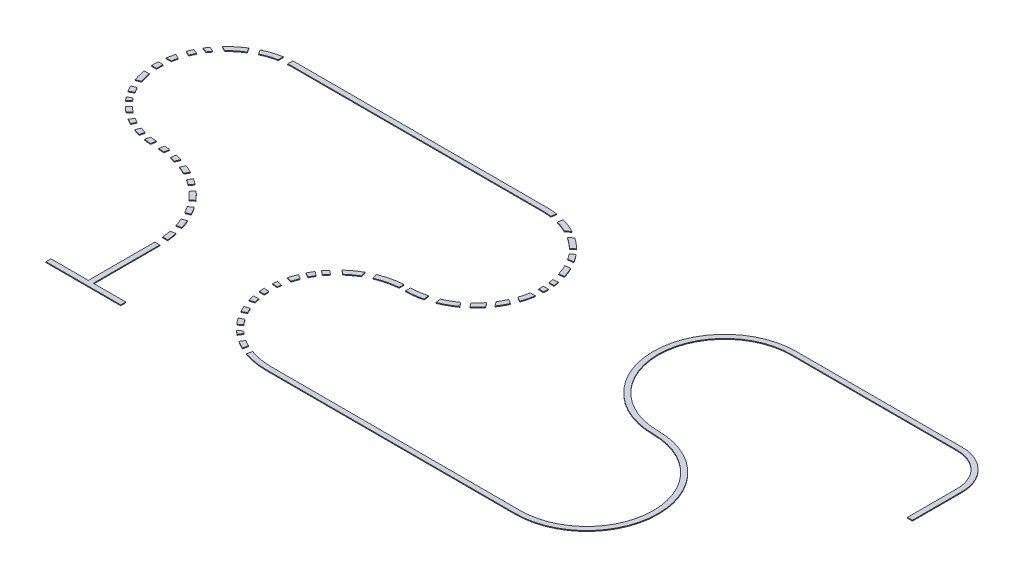
SolidWorks part; units mm, degrees
ref_plane "Front Plane" through (0, 0, 0) normal (0, 0, 1) x (1, 0, 0)
ref_plane "Top Plane" through (0, 0, 0) normal (0, 1, 0) x (1, 0, 0)
ref_plane "Right Plane" through (0, 0, 0) normal (1, 0, 0) x (0, 0, -1)
sketch "Sketch1" plane through (0, 0, 0) normal (0, 1, 0) x (1, 0, 0)
  line L0 (0, 0) -> (-450, 0)
  line L1 (-450, 0) -> (-450, 30)
  line L2 (-450, 30) -> (-225, 30)
  line L3 (-225, 30) -> (-225, 430)
  line L4 (0, 0) -> (0, 30)
  line L5 (0, 30) -> (-195, 30)
  line L6 (-195, 30) -> (-195, 430)
  line L7 (-725, 1790) -> (775, 1790)
  line L8 (-725, 1760) -> (775, 1760)
  line L9 (775, 130) -> (2275, 130)
  line L10 (2275, 1790) -> (3275, 1790)
  line L11 (775, 100) -> (2275, 100)
  line L12 (2275, 1760) -> (3275, 1760)
  line L14 (3475, 1560) -> (3475, 1260)
  line L17 (3475, 1260) -> (3505, 1260)
  line L18 (3505, 1260) -> (3505, 1560)
  arc A0 (-225, 430) -> (-725, 930) centre (-725, 430) ccw
  arc A1 (-195, 430) -> (-725, 960) centre (-725, 430) ccw
  arc A2 (-725, 960) -> (-725, 1760) centre (-725, 1360) cw
  arc A3 (-725, 930) -> (-725, 1790) centre (-725, 1360) cw
  arc A4 (775, 1760) -> (775, 960) centre (775, 1360) cw
  arc A5 (775, 960) -> (775, 100) centre (775, 530) ccw
  arc A6 (775, 1790) -> (775, 930) centre (775, 1360) cw
  arc A7 (775, 930) -> (775, 130) centre (775, 530) ccw
  arc A8 (2275, 130) -> (2275, 930) centre (2275, 530) ccw
  arc A9 (2275, 930) -> (2275, 1790) centre (2275, 1360) cw
  arc A10 (2275, 100) -> (2275, 960) centre (2275, 530) ccw
  arc A11 (2275, 960) -> (2275, 1760) centre (2275, 1360) cw
  arc A12 (3275, 1760) -> (3475, 1560) centre (3275, 1560) cw
  arc A14 (3275, 1790) -> (3505, 1560) centre (3275, 1560) cw
  dimension "D5" = 500
  dimension "D6" = 530
  dimension "D7" = 30
  dimension "D9" = 400
  dimension "D10" = 430
  dimension "D11" = 30
  dimension "D12" = 90
  dimension "D15" = 400
  dimension "D16" = 430
  dimension "D17" = 400
  dimension "D18" = 430
  dimension "D19" = 400
  dimension "D20" = 430
  dimension "D21" = 400
  dimension "D22" = 430
  dimension "D25" = 200
  dimension "D26" = 230
  dimension "D28" = 30
  dimension "D1" = 225
  dimension "D2" = 30
  dimension "D3" = 450
  dimension "D4" = 30
  dimension "D8" = 400
  dimension "D13" = 1500
  dimension "D14" = 1500
  dimension "D23" = 1500
  dimension "D24" = 1000
  dimension "D27" = 30
  dimension "D29" = 300
extrude "Boss-Extrude1" add sketch "Sketch1" along normal blind 5
sketch "Sketch4" plane through (0, 5, 0) normal (0, 1, 0) x (1, 0, 0)
  line L0 (-225, 30) -> (-450, 30) construction
  line L1 (-195, 430) -> (-245.0712, 430)
  line L2 (-195, 430) -> (-195, 480)
  line L3 (-195, 480) -> (-245.0712, 480)
  line L4 (-245.0712, 430) -> (-245.0712, 480)
  line L9 (-247.1885, 529.9552) -> (-200.4396, 539.625)
  line L10 (-247.1885, 529.9552) -> (-257.3164, 578.9187)
  line L11 (-200.4396, 539.625) -> (-210.5675, 588.5885)
  line L12 (-257.3164, 578.9187) -> (-210.5675, 588.5885)
  line L13 (-220.767, 646.8807) -> (-298.6651, 615.9153)
  line L14 (-220.767, 646.8807) -> (-239.2368, 693.3443)
  line L15 (-298.6651, 615.9153) -> (-317.1349, 662.3789)
  line L16 (-239.2368, 693.3443) -> (-317.1349, 662.3789)
  line L17 (-363.7418, 824.7943) -> (-395.8009, 785.4802)
  line L18 (-363.7418, 824.7943) -> (-402.4912, 856.393)
  line L19 (-395.8009, 785.4802) -> (-434.5504, 817.0789)
  line L20 (-402.4912, 856.393) -> (-434.5504, 817.0789)
  line L21 (-434.1844, 884.8161) -> (-460.0898, 838.9017)
  line L22 (-434.1844, 884.8161) -> (-477.7312, 909.3858)
  line L23 (-460.0898, 838.9017) -> (-503.6367, 863.4714)
  line L24 (-477.7312, 909.3858) -> (-503.6367, 863.4714)
  line L25 (-610.7355, 967.3673) -> (-624.0514, 882.3992)
  line L26 (-610.7355, 967.3673) -> (-660.1326, 975.1086)
  line L27 (-624.0514, 882.3992) -> (-673.4485, 890.1405)
  line L28 (-660.1326, 975.1086) -> (-673.4485, 890.1405)
  line L29 (-908.3575, 1038.2893) -> (-960.9177, 973.8348)
  line L30 (-908.3575, 1038.2893) -> (-947.107, 1069.888)
  line L31 (-960.9177, 973.8348) -> (-999.6672, 1005.4335)
  line L32 (-947.107, 1069.888) -> (-999.6672, 1005.4335)
  line L33 (-1049.8135, 1195.8302) -> (-1135.1772, 1161.8971)
  line L34 (-1049.8135, 1195.8302) -> (-1068.2833, 1242.2938)
  line L35 (-1135.1772, 1161.8971) -> (-1153.647, 1208.3607)
  line L36 (-1068.2833, 1242.2938) -> (-1153.647, 1208.3607)
  line L37 (-1087.5125, 1290.6677) -> (-1186.365, 1290.6677)
  line L38 (-1087.5125, 1290.6677) -> (-1087.5125, 1340.6677)
  line L39 (-1186.365, 1290.6677) -> (-1186.365, 1340.6677)
  line L40 (-1087.5125, 1340.6677) -> (-1186.365, 1340.6677)
  line L41 (-1031.1644, 1418.2648) -> (-1180.5491, 1490.6232)
  line L42 (-1031.1644, 1418.2648) -> (-1009.3679, 1463.2638)
  line L43 (-1180.5491, 1490.6232) -> (-1158.7527, 1535.6222)
  line L44 (-1009.3679, 1463.2638) -> (-1158.7527, 1535.6222)
  line L45 (-1101.7345, 1625.9972) -> (-1008.7159, 1580.9413)
  line L46 (-1101.7345, 1625.9972) -> (-1079.938, 1670.9963)
  line L47 (-1008.7159, 1580.9413) -> (-986.9195, 1625.9403)
  line L48 (-1079.938, 1670.9963) -> (-986.9195, 1625.9403)
  line L49 (-973.0242, 1755.1283) -> (-924.0801, 1677.1552)
  line L50 (-973.0242, 1755.1283) -> (-930.6758, 1781.7106)
  line L51 (-924.0801, 1677.1552) -> (-881.7317, 1703.7375)
  line L52 (-930.6758, 1781.7106) -> (-881.7317, 1703.7375)
  line L53 (-804.133, 1806.7944) -> (-804.133, 1713.8119)
  line L54 (-804.133, 1806.7944) -> (-754.133, 1806.7944)
  line L55 (-804.133, 1713.8119) -> (-754.133, 1713.8119)
  line L56 (-754.133, 1806.7944) -> (-754.133, 1713.8119)
  line L181 (-324.6529, 701.5951) -> (-278.6431, 739.1523)
  line L182 (-324.6529, 701.5951) -> (-356.2708, 740.3289)
  line L183 (-278.6431, 739.1523) -> (-310.2611, 777.886)
  line L184 (-356.2708, 740.3289) -> (-310.2611, 777.886)
  line L185 (-571.0443, 951.3691) -> (-593.9884, 895.3838)
  line L186 (-571.0443, 951.3691) -> (-524.7788, 932.4084)
  line L187 (-593.9884, 895.3838) -> (-547.7229, 876.4231)
  line L188 (-524.7788, 932.4084) -> (-547.7229, 876.4231)
  line L189 (-692.8161, 981.8642) -> (-704.1747, 909.3858)
  line L190 (-692.8161, 981.8642) -> (-741.8578, 989.5498)
  line L191 (-704.1747, 909.3858) -> (-753.2163, 917.0714)
  line L192 (-741.8578, 989.5498) -> (-753.2163, 917.0714)
  line L193 (-778.723, 989.5498) -> (-795.0574, 917.0714)
  line L194 (-778.723, 989.5498) -> (-820.2357, 998.9055)
  line L195 (-795.0574, 917.0714) -> (-836.5701, 926.4271)
  line L196 (-820.2357, 998.9055) -> (-836.5701, 926.4271)
  line L197 (-849.2014, 1005.4335) -> (-883.9893, 926.4271)
  line L198 (-849.2014, 1005.4335) -> (-892.792, 1024.6272)
  line L199 (-883.9893, 926.4271) -> (-927.5798, 945.6208)
  line L200 (-892.792, 1024.6272) -> (-927.5798, 945.6208)
  line L201 (-1030.3623, 1038.2893) -> (-989.3745, 1081.1044)
  line L202 (-1030.3623, 1038.2893) -> (-1060.7794, 1067.4084)
  line L203 (-989.3745, 1081.1044) -> (-1019.7916, 1110.2234)
  line L204 (-1060.7794, 1067.4084) -> (-1019.7916, 1110.2234)
  line L205 (-1076.2783, 1096.1807) -> (-1030.3623, 1121.7853)
  line L206 (-1076.2783, 1096.1807) -> (-1097.2008, 1133.7005)
  line L207 (-1030.3623, 1121.7853) -> (-1051.2848, 1159.3051)
  line L208 (-1097.2008, 1133.7005) -> (-1051.2848, 1159.3051)
  line L209 (-1097.2008, 1379.9043) -> (-1180.5491, 1379.9043)
  line L210 (-1097.2008, 1379.9043) -> (-1097.2008, 1423.9331)
  line L211 (-1180.5491, 1379.9043) -> (-1180.5491, 1423.9331)
  line L212 (-1097.2008, 1423.9331) -> (-1180.5491, 1423.9331)
  line L213 (-1138.875, 1560.8592) -> (-1060.7794, 1531.5477)
  line L214 (-1138.875, 1560.8592) -> (-1124.6056, 1598.8776)
  line L215 (-1060.7794, 1531.5477) -> (-1046.51, 1569.5661)
  line L216 (-1124.6056, 1598.8776) -> (-1046.51, 1569.5661)
  line L217 (845.8025, 1822.913) -> (820.577, 1703.7375)
  line L218 (845.8025, 1822.913) -> (896.0493, 1812.2774)
  line L219 (820.577, 1703.7375) -> (870.8238, 1693.1019)
  line L220 (896.0493, 1812.2774) -> (870.8238, 1693.1019)
  line L221 (913.5823, 1693.0912) -> (993.4468, 1754.0785)
  line L222 (913.5823, 1693.0912) -> (941.3299, 1656.7549)
  line L223 (993.4468, 1754.0785) -> (1021.1944, 1717.7421)
  line L224 (941.3299, 1656.7549) -> (1021.1944, 1717.7421)
  line L225 (1030.0198, 1625.8338) -> (1091.7109, 1672.9432)
  line L226 (1030.0198, 1625.8338) -> (1054.7697, 1593.4231)
  line L227 (1091.7109, 1672.9432) -> (1116.4608, 1640.5326)
  line L228 (1054.7697, 1593.4231) -> (1116.4608, 1640.5326)
  line L229 (1085.6509, 1580.9284) -> (1162.9893, 1591.2282)
  line L230 (1085.6509, 1580.9284) -> (1091.7038, 1535.4786)
  line L231 (1162.9893, 1591.2282) -> (1169.0423, 1545.7785)
  line L232 (1091.7038, 1535.4786) -> (1169.0423, 1545.7785)
  line L233 (1131.5968, 1476.0362) -> (1202.6193, 1485.4949)
  line L234 (1131.5968, 1476.0362) -> (1137.9834, 1428.0817)
  line L235 (1202.6193, 1485.4949) -> (1209.0058, 1437.5404)
  line L236 (1137.9834, 1428.0817) -> (1209.0058, 1437.5404)
  line L237 (1139.6192, 1340.6677) -> (1227.8267, 1340.6677)
  line L238 (1139.6192, 1340.6677) -> (1139.6192, 1294.9464)
  line L239 (1227.8267, 1340.6677) -> (1227.8267, 1294.9464)
  line L240 (1139.6192, 1294.9464) -> (1227.8267, 1294.9464)
  line L241 (1139.6192, 1405.0079) -> (1227.8267, 1405.0079)
  line L242 (1139.6192, 1405.0079) -> (1139.6192, 1368.8535)
  line L243 (1227.8267, 1405.0079) -> (1227.8267, 1368.8535)
  line L244 (1139.6192, 1368.8535) -> (1227.8267, 1368.8535)
  line L245 (1125.9303, 1252.8071) -> (1209.8067, 1203.457)
  line L246 (1125.9303, 1252.8071) -> (1104.5247, 1216.4258)
  line L247 (1209.8067, 1203.457) -> (1188.4012, 1167.0757)
  line L248 (1104.5247, 1216.4258) -> (1188.4012, 1167.0757)
  line L249 (1091.0805, 1174.2122) -> (1144.8166, 1103.8433)
  line L250 (1091.0805, 1174.2122) -> (1060.7085, 1151.0191)
  line L251 (1144.8166, 1103.8433) -> (1114.4445, 1080.6502)
  line L252 (1060.7085, 1151.0191) -> (1114.4445, 1080.6502)
  line L253 (1031.2993, 1079.7749) -> (1076.2701, 1020.8845)
  line L254 (1031.2993, 1079.7749) -> (996.6797, 1053.3382)
  line L255 (1076.2701, 1020.8845) -> (1041.6504, 994.4478)
  line L256 (996.6797, 1053.3382) -> (1041.6504, 994.4478)
  line L257 (927.7063, 1024.1895) -> (941.8165, 918.2403)
  line L258 (927.7063, 1024.1895) -> (872.8536, 1016.8843)
  line L259 (941.8165, 918.2403) -> (886.9638, 910.935)
  line L260 (872.8536, 1016.8843) -> (886.9638, 910.935)
  line L261 (784.0122, 995.0408) -> (784.0122, 884.8161)
  line L262 (784.0122, 995.0408) -> (746.0309, 995.0408)
  line L263 (784.0122, 884.8161) -> (746.0309, 884.8161)
  line L264 (746.0309, 995.0408) -> (746.0309, 884.8161)
  line L265 (600.6456, 963.9097) -> (631.949, 856.393)
  line L266 (600.6456, 963.9097) -> (551.4192, 949.5774)
  line L267 (631.949, 856.393) -> (582.7226, 842.0608)
  line L268 (551.4192, 949.5774) -> (582.7226, 842.0608)
  line L269 (462.9108, 863.4714) -> (533.0303, 808.6993)
  line L270 (462.9108, 863.4714) -> (431.0604, 822.6964)
  line L271 (533.0303, 808.6993) -> (501.18, 767.9243)
  line L272 (431.0604, 822.6964) -> (501.18, 767.9243)
  line L273 (409.6685, 795.3104) -> (481.5625, 739.1523)
  line L274 (409.6685, 795.3104) -> (392.5282, 773.3673)
  line L275 (481.5625, 739.1523) -> (464.4222, 717.2091)
  line L276 (392.5282, 773.3673) -> (464.4222, 717.2091)
  line L277 (365.802, 739.1523) -> (443.6582, 693.3443)
  line L278 (365.802, 739.1523) -> (348.3183, 709.4365)
  line L279 (443.6582, 693.3443) -> (426.1745, 663.6285)
  line L280 (348.3183, 709.4365) -> (426.1745, 663.6285)
  line L281 (337.6973, 646.8807) -> (404.7301, 632.6921)
  line L282 (337.6973, 646.8807) -> (327.4116, 598.287)
  line L283 (404.7301, 632.6921) -> (394.4444, 584.0983)
  line L284 (327.4116, 598.287) -> (394.4444, 584.0983)
  line L285 (327.4116, 570.1317) -> (394.4444, 562.4065)
  line L286 (327.4116, 570.1317) -> (321.7973, 521.4156)
  line L287 (394.4444, 562.4065) -> (388.8302, 513.6904)
  line L288 (321.7973, 521.4156) -> (388.8302, 513.6904)
  line L289 (327.4116, 487.5221) -> (388.8302, 487.5221)
  line L290 (327.4116, 487.5221) -> (327.4116, 446.8206)
  line L291 (388.8302, 487.5221) -> (388.8302, 446.8206)
  line L292 (327.4116, 446.8206) -> (388.8302, 446.8206)
  line L293 (348.3183, 406.8209) -> (404.7301, 423.2451)
  line L294 (348.3183, 406.8209) -> (362.5046, 358.0955)
  line L295 (404.7301, 423.2451) -> (418.9165, 374.5198)
  line L296 (362.5046, 358.0955) -> (418.9165, 374.5198)
  line L297 (376.5242, 317.5238) -> (434.9164, 347.4264)
  line L298 (376.5242, 317.5238) -> (399.35, 272.9509)
  line L299 (434.9164, 347.4264) -> (457.7421, 302.8535)
  line L300 (399.35, 272.9509) -> (457.7421, 302.8535)
  line L301 (434.9164, 237.3303) -> (481.5625, 272.9509)
  line L302 (434.9164, 237.3303) -> (462.5405, 201.1557)
  line L303 (481.5625, 272.9509) -> (509.1866, 236.7763)
  line L304 (462.5405, 201.1557) -> (509.1866, 236.7763)
  line L305 (495.3746, 181.1007) -> (523.2422, 228.4652)
  line L306 (495.3746, 181.1007) -> (540.283, 154.6781)
  line L307 (523.2422, 228.4652) -> (568.1506, 202.0426)
  line L308 (540.283, 154.6781) -> (568.1506, 202.0426)
  line L309 (600.6456, 186.3599) -> (587.9974, 126.6046)
  line L310 (600.6456, 186.3599) -> (644.7096, 177.033)
  line L311 (587.9974, 126.6046) -> (632.0613, 117.2777)
  line L312 (644.7096, 177.033) -> (632.0613, 117.2777)
  arc A0 (-195, 430) -> (-725, 960) centre (-725, 430) ccw construction
  dimension "D1" = 50
  dimension "D2" = 50.0712
  dimension "D3" = 400
  dimension "D4" = 50
  dimension "D7" = 50
  dimension "D8" = 50
  dimension "D9" = 50
  dimension "D10" = 50
  dimension "D11" = 50
  dimension "D12" = 50
  dimension "D13" = 50
  dimension "D14" = 50
  dimension "D15" = 50
  dimension "D16" = 50
  dimension "D17" = 50
  dimension "D18" = 50
  dimension "D19" = 50
  dimension "D20" = 50
extrude "Cut-Extrude1" cut sketch "Sketch4" against normal up to next (5 mm away)
